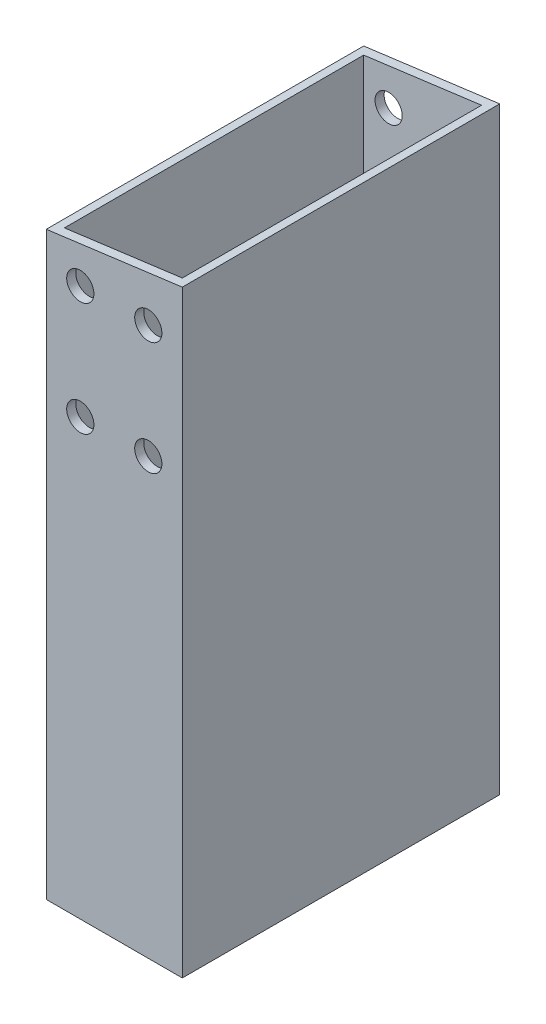
SolidWorks part; units mm, degrees
ref_plane "前视基准面" through (0, 0, 0) normal (0, 0, 1) x (1, 0, 0)
ref_plane "上视基准面" through (0, 0, 0) normal (0, 1, 0) x (1, 0, 0)
ref_plane "右视基准面" through (0, 0, 0) normal (1, 0, 0) x (0, 0, -1)
other "Configuration Table"
sketch "草图1" plane through (0, 0, 0) normal (0, 0, 1) x (1, 0, 0)
  line L1 (15, -375) -> (-15, -375)
  line L2 (15, -375) -> (15, 375)
  line L3 (15, 375) -> (-15, 375)
  line L4 (-15, -375) -> (-15, 375)
  line L5 (15, -375) -> (-15, 375) construction
  line L6 (15, 375) -> (-15, -375) construction
  circle A0 centre (-7.5, 363.9688) radius 2
  circle A2 centre (7.5, 363.9688) radius 2
  circle A3 centre (-7.5, 338.9688) radius 2
  circle A4 centre (7.5, 338.9688) radius 2
  circle A5 centre (-7.5, -312.8679) radius 2
  circle A6 centre (7.5, -312.8679) radius 2
  circle A7 centre (-7.5, -337.8679) radius 2
  circle A8 centre (7.5, -337.8679) radius 2
  point P0 (0, 0)
  dimension "D1" = 30
  dimension "D2" = 750
extrude "凸台-拉伸2" add sketch "草图1" along normal blind 70
sketch "草图2" plane through (0, -375, 0) normal (0, -1, 0) x (1, 0, 0)
  line L0 (-15, 70) -> (-15, 0) construction
  line L1 (-13, 68) -> (13, 68)
  line L2 (-13, 68) -> (-13, 2)
  line L3 (-13, 2) -> (13, 2)
  line L4 (13, 68) -> (13, 2)
  line L5 (-13, 68) -> (13, 2) construction
  line L6 (-13, 2) -> (13, 68) construction
  line L7 (-15, 70) -> (15, 70) construction
  line L8 (15, 70) -> (15, 0) construction
  line L9 (-15, 0) -> (15, 0) construction
  point P0 (0, 35)
  dimension "D1" = 2
  dimension "D2" = 2
  dimension "D3" = 2
  dimension "D4" = 2
extrude "切除-拉伸3" cut sketch "草图2" against normal through all contours L2 L1 L4 L3
sketch "草图3" plane through (0, 0, 70) normal (0, 0, 1) x (1, 0, 0)
  line L0 (15, 375) -> (-15, 371.0504)
  line L1 (-15, 375) -> (-15, -375) construction
  line L2 (15, -375) -> (15, 375) construction
  line L3 (15, -347.1) -> (-15, -343.1504)
  line L4 (-15, -343.1504) -> (-15, -376.6872)
  line L5 (-15, -376.6872) -> (15, -376.6872)
  line L6 (15, -376.6872) -> (15, -347.1)
  line L7 (-15, 371.0504) -> (-15, 377.0408)
  line L8 (-15, 377.0408) -> (15, 377.0408)
  line L9 (15, 377.0408) -> (15, 375)
  line M2 (-15, 375) -> (-15, -375)
  line M3 (-15, -375) -> (15, -375)
  line M4 (15, -375) -> (15, 375)
  dimension "D1" = 82.5
  dimension "D2" = 82.5
  dimension "D3" = 722.1
extrude "切除-拉伸4" cut sketch "草图3" against normal through all contours L3 M4 M2 M3 | L9 L0 L7 L8
sketch "草图4" plane through (0, 0, 0) normal (0, 0, -1) x (-1, 0, 0)
  line L0 (-15, 243.0504) -> (15, 243.0504)
  line L1 (-15, -347.1) -> (-15, 375) construction
  line L2 (15, 371.0504) -> (15, -343.1504) construction
  line L3 (-15, 243.0504) -> (-15, -679.8701)
  line L4 (-15, -679.8701) -> (15, -679.8701)
  line L5 (15, -679.8701) -> (15, 243.0504)
  dimension "D1" = 128
extrude "切除-拉伸5" cut sketch "草图4" against normal through all
sketch "草图5" plane through (0, 0, 70) normal (0, 0, 1) x (1, 0, 0)
  circle A0 centre (-7.5, 363.9688) radius 3
  circle A1 centre (7.5, 363.9688) radius 3
  circle A2 centre (7.5, 338.9688) radius 3
  circle A3 centre (-7.5, 338.9688) radius 3
  dimension "D1" = 6
  dimension "D2" = 6
  dimension "D3" = 6
  dimension "D4" = 6
extrude "切除-拉伸6" cut sketch "草图5" against normal blind 91
